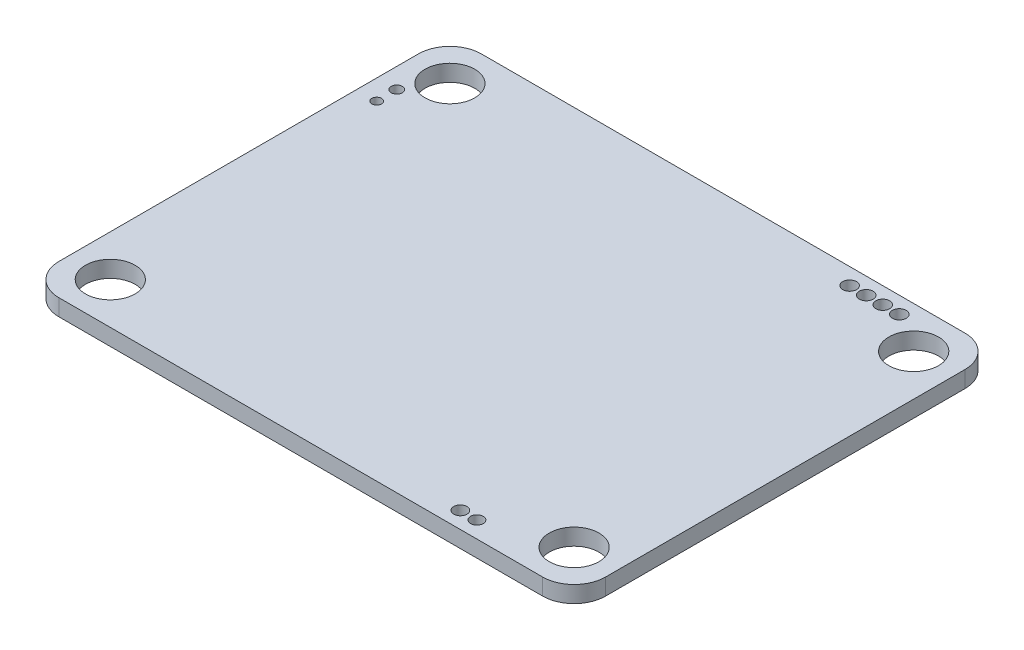
SolidWorks part; units mm, degrees
ref_plane "Front Plane" through (0, 0, 0) normal (0, 0, 1) x (1, 0, 0)
ref_plane "Top Plane" through (0, 0, 0) normal (0, 1, 0) x (1, 0, 0)
ref_plane "Right Plane" through (0, 0, 0) normal (1, 0, 0) x (0, 0, -1)
sketch "Sketch1" plane through (0, 5.2595, 0) normal (0, -1, 0) x (1, 0, 0)
  line L0 (70.717, 148.7978) -> (7.1417, 148.7978) construction
  line L1 (70.717, 174.2978) -> (4.717, 174.2978)
  line L2 (70.717, 174.2978) -> (70.717, 123.2978)
  line L3 (70.717, 123.2978) -> (4.717, 123.2978)
  line L4 (4.717, 174.2978) -> (4.717, 123.2978)
  line L5 (37.717, 123.2978) -> (37.717, 174.2978) construction
  line L6 (9.717, 125.2978) -> (65.717, 125.2978) construction
  line L7 (65.717, 172.2978) -> (33.9771, 172.2978) construction
  circle A0 centre (65.717, 128.2978) radius 3
  circle A1 centre (9.717, 128.2978) radius 3
  circle A2 centre (65.717, 169.2978) radius 3
  circle A3 centre (9.717, 169.2978) radius 3
  circle A4 centre (60.9813, 125.2978) radius 0.8374
  circle A5 centre (58.9813, 125.2978) radius 0.8374
  circle A6 centre (56.9813, 125.2978) radius 0.8374
  circle A7 centre (54.9813, 125.2978) radius 0.8374
  circle A8 centre (56.9813, 172.2978) radius 0.7641
  circle A9 centre (54.9813, 172.2978) radius 0.8032
  circle A10 centre (7.1417, 132.1348) radius 0.6733
  circle A11 centre (7.1417, 134.5599) radius 0.5891
  dimension "D1" = 66
  dimension "D3" = 6
  dimension "D5" = 5
  dimension "D2" = 51
  dimension "D4" = 5
  dimension "D6" = 4
extrude "Boss-Extrude1" add sketch "Sketch1" along normal blind 2
fillet "Fillet1" radius 3.8 4 edges at (4.717, 4.2595, 174.2978) (4.717, 4.2595, 123.2978) (70.717, 4.2595, 174.2978) (70.717, 4.2595, 123.2978)
sketch "Sketch2" plane through (0, 3.2595, 0) normal (0, -1, 0) x (1, 0, 0)
  line L0 (4.717, 148.7978) -> (13.8206, 148.7978) construction
  line L1 (4.717, 170.4978) -> (4.717, 127.0978) construction
  line L3 (12.187, 163.1018) -> (6.3506, 163.1018)
  line L4 (12.187, 163.1018) -> (12.187, 134.4937)
  line L5 (12.187, 134.4937) -> (6.3506, 134.4937)
  line L6 (6.3506, 163.1018) -> (6.3506, 134.4937)
  line L7 (12.187, 163.1018) -> (6.3506, 134.4937) construction
  line L8 (12.187, 134.4937) -> (6.3506, 163.1018) construction
  point P4 (9.2688, 148.7978)
extrude "Boss-Extrude2" add sketch "Sketch2" along normal blind 1
sketch "Sketch3" plane through (0, 2.2595, 0) normal (0, -1, 0) x (1, 0, 0)
  line L0 (12.187, 163.1018) -> (6.3506, 163.1018) construction
  line L1 (12.187, 134.4937) -> (7.8424, 134.4937)
  line L2 (12.187, 134.4937) -> (12.187, 163.1018)
  line L3 (12.187, 163.1018) -> (7.8424, 163.1018)
  line L4 (7.8424, 134.4937) -> (7.8424, 163.1018)
extrude "Boss-Extrude3" add sketch "Sketch3" along normal blind 1
sketch "Sketch4" plane through (0, 3.2595, 0) normal (0, -1, 0) x (1, 0, 0)
  line L0 (51.6149, 157.4624) -> (51.6149, 161.23)
  line L1 (33.3084, 134.3107) -> (22.8131, 134.3107)
  line L2 (33.3084, 134.3107) -> (33.3084, 148.7869)
  line L3 (33.3084, 148.7869) -> (22.8131, 148.7869)
  line L4 (22.8131, 134.3107) -> (22.8131, 148.7869)
  line L5 (22.1557, 165.5193) -> (19.2014, 165.5193)
  line L6 (22.1557, 165.5193) -> (22.1557, 169.9814)
  line L7 (22.1557, 169.9814) -> (19.2014, 169.9814)
  line L8 (19.2014, 165.5193) -> (19.2014, 169.9814)
  line L9 (50.1502, 170.8666) -> (55.0928, 170.8666)
  line L10 (50.1502, 170.8666) -> (50.1502, 167.7504)
  line L11 (50.1502, 167.7504) -> (55.0928, 167.7504)
  line L12 (55.0928, 170.8666) -> (55.0928, 167.7504)
  line L13 (54.7615, 157.4624) -> (53.6149, 157.4624)
  line L14 (54.7615, 157.4624) -> (54.7615, 161.23)
  line L15 (54.7615, 161.23) -> (53.6149, 161.23)
  line L16 (53.6149, 157.4624) -> (53.6149, 161.23)
  line L17 (52.7615, 157.4624) -> (52.7615, 161.23)
  line L18 (52.7615, 157.4624) -> (51.6149, 157.4624)
  line L19 (52.7615, 161.23) -> (51.6149, 161.23)
  line L20 (49.6149, 157.4624) -> (49.6149, 161.23)
  line L21 (50.7615, 157.4624) -> (50.7615, 161.23)
  line L22 (50.7615, 157.4624) -> (49.6149, 157.4624)
  line L23 (50.7615, 161.23) -> (49.6149, 161.23)
  line L24 (47.6149, 157.4624) -> (47.6149, 161.23)
  line L25 (48.7615, 157.4624) -> (48.7615, 161.23)
  line L26 (48.7615, 157.4624) -> (47.6149, 157.4624)
  line L27 (48.7615, 161.23) -> (47.6149, 161.23)
  line L28 (45.6149, 157.4624) -> (45.6149, 161.23)
  line L29 (46.7615, 157.4624) -> (46.7615, 161.23)
  line L30 (46.7615, 157.4624) -> (45.6149, 157.4624)
  line L31 (46.7615, 161.23) -> (45.6149, 161.23)
  line L32 (43.6149, 157.4624) -> (43.6149, 161.23)
  line L33 (44.7615, 157.4624) -> (44.7615, 161.23)
  line L34 (44.7615, 157.4624) -> (43.6149, 157.4624)
  line L35 (44.7615, 161.23) -> (43.6149, 161.23)
  line L36 (41.6149, 157.4624) -> (41.6149, 161.23)
  line L37 (42.7615, 157.4624) -> (42.7615, 161.23)
  line L38 (42.7615, 157.4624) -> (41.6149, 157.4624)
  line L39 (42.7615, 161.23) -> (41.6149, 161.23)
  line L40 (39.6149, 157.4624) -> (39.6149, 161.23)
  line L41 (40.7615, 157.4624) -> (40.7615, 161.23)
  line L42 (40.7615, 157.4624) -> (39.6149, 157.4624)
  line L43 (40.7615, 161.23) -> (39.6149, 161.23)
  line L44 (37.6149, 157.4624) -> (37.6149, 161.23)
  line L45 (38.7615, 157.4624) -> (38.7615, 161.23)
  line L46 (38.7615, 157.4624) -> (37.6149, 157.4624)
  line L47 (38.7615, 161.23) -> (37.6149, 161.23)
  line L48 (35.6149, 157.4624) -> (35.6149, 161.23)
  line L49 (36.7615, 157.4624) -> (36.7615, 161.23)
  line L50 (36.7615, 157.4624) -> (35.6149, 157.4624)
  line L51 (36.7615, 161.23) -> (35.6149, 161.23)
  line L52 (21.8764, 124.7735) -> (23.1698, 124.7735)
  line L53 (16.8764, 124.7735) -> (18.1698, 124.7735)
  line L54 (16.8764, 124.7735) -> (16.8764, 128.5218)
  line L55 (16.8764, 128.5218) -> (18.1698, 128.5218)
  line L56 (18.1698, 124.7735) -> (18.1698, 128.5218)
  line L57 (23.1698, 124.7735) -> (23.1698, 128.5218)
  line L58 (21.8764, 128.5218) -> (23.1698, 128.5218)
  line L59 (21.8764, 124.7735) -> (21.8764, 128.5218)
  line L60 (26.8764, 124.7735) -> (28.1698, 124.7735)
  line L61 (28.1698, 124.7735) -> (28.1698, 128.5218)
  line L62 (26.8764, 128.5218) -> (28.1698, 128.5218)
  line L63 (26.8764, 124.7735) -> (26.8764, 128.5218)
  line L64 (31.8764, 124.7735) -> (33.1698, 124.7735)
  line L65 (33.1698, 124.7735) -> (33.1698, 128.5218)
  line L66 (31.8764, 128.5218) -> (33.1698, 128.5218)
  line L67 (31.8764, 124.7735) -> (31.8764, 128.5218)
  line L68 (36.8764, 124.7735) -> (38.1698, 124.7735)
  line L69 (38.1698, 124.7735) -> (38.1698, 128.5218)
  line L70 (36.8764, 128.5218) -> (38.1698, 128.5218)
  line L71 (36.8764, 124.7735) -> (36.8764, 128.5218)
  circle A0 centre (29.7562, 164.2612) radius 1.6229
  dimension "D1" = 10
  dimension "D2" = 5
extrude "Boss-Extrude4" add sketch "Sketch4" along normal blind 1
